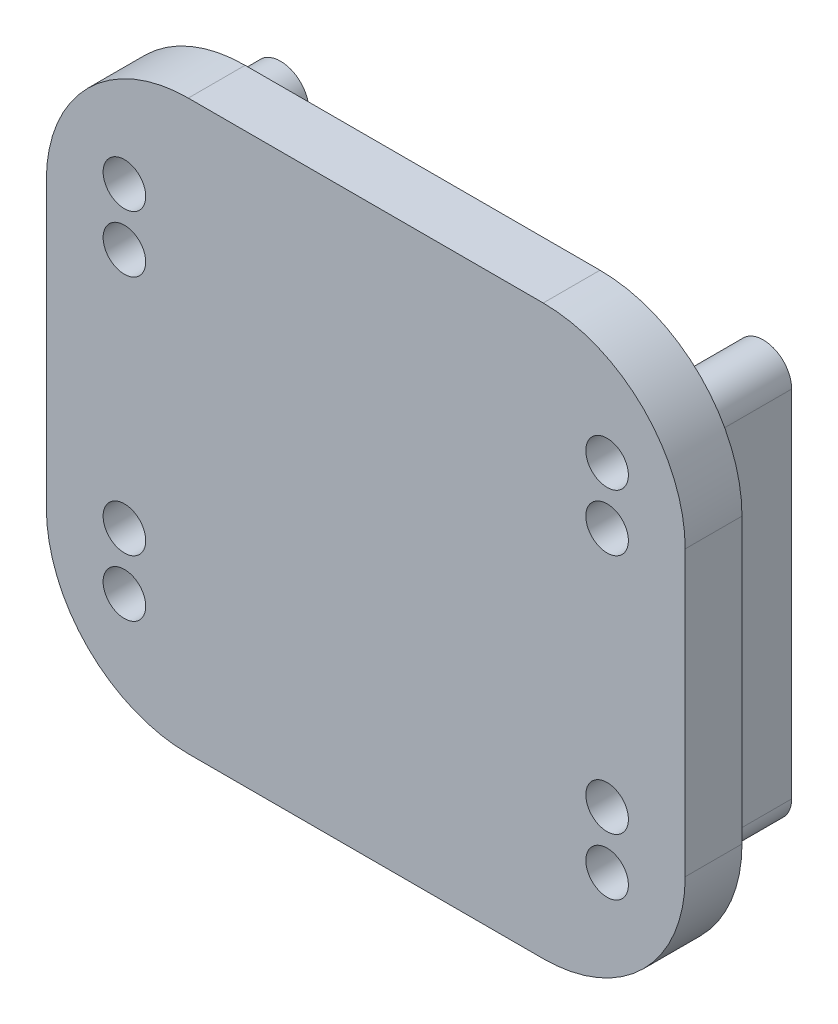
SolidWorks part; units mm, degrees
ref_plane "Front Plane" through (0, 0, 0) normal (0, 0, 1) x (1, 0, 0)
ref_plane "Top Plane" through (0, 0, 0) normal (0, 1, 0) x (1, 0, 0)
ref_plane "Right Plane" through (0, 0, 0) normal (1, 0, 0) x (0, 0, -1)
sketch "Sketch1" plane through (0, 0, 0) normal (0, 0, 1) x (1, 0, 0)
  line L0 (0, 0) -> (0, 25)
  line L1 (30, 0) -> (30, 25)
  line L2 (-4, 25) -> (-4, 0)
  line L3 (34, 25) -> (34, 0)
  arc A0 (-4, 25) -> (0, 25) centre (-2, 25) cw
  arc A1 (-4, 0) -> (0, 0) centre (-2, 0) ccw
  arc A2 (34, 25) -> (30, 25) centre (32, 25) ccw
  arc A3 (34, 0) -> (30, 0) centre (32, 0) cw
  dimension "D1" = 25
  dimension "D2" = 30
  dimension "D3" = 4
  dimension "D4" = 4
extrude "Boss-Extrude1" add sketch "Sketch1" along normal blind 7
sketch "Sketch2" plane through (0, 0, 7) normal (0, 0, 1) x (1, 0, 0)
  line L0 (-4, 12.5) -> (34, 12.5) construction
  line L5 (-4, 25) -> (-4, 0) construction
  line L6 (34, 0) -> (34, 25) construction
  line L8 (-7.5, -7.5) -> (37.5, -7.5)
  line L9 (-7.5, -7.5) -> (-7.5, 32.5)
  line L10 (-7.5, 32.5) -> (37.5, 32.5)
  line L11 (37.5, -7.5) -> (37.5, 32.5)
  line L12 (-7.5, -7.5) -> (37.5, 32.5) construction
  line L13 (-7.5, 32.5) -> (37.5, -7.5) construction
  point P0 (15, 12.5)
  point P10 (15, 12.5)
  dimension "D1" = 45
  dimension "D2" = 40
extrude "Boss-Extrude2" add sketch "Sketch2" along normal blind 4
fillet "Fillet1" radius 10 4 edges at (-7.5, 32.5, 9) (37.5, 32.5, 9) (-7.5, -7.5, 9) (37.5, -7.5, 9)
sketch "Sketch3" plane through (0, 0, 0) normal (0, 0, -1) x (-1, 0, 0)
  line L0 (0, 12.5) -> (-30, 12.5) construction
  line L1 (0, 0) -> (0, 25) construction
  line L2 (-30, 25) -> (-30, 0) construction
  circle A0 centre (-32, 0) radius 1.5
  arc A1 (-34, 0) -> (-30, 0) centre (-32, 0) ccw construction
  circle A4 centre (-32, 4) radius 1.5
  circle A5 centre (2, 0) radius 1.5
  arc A6 (0, 0) -> (4, 0) centre (2, 0) ccw construction
  circle A7 centre (2, 4) radius 1.5
  circle A8 centre (-32, 25) radius 1.5
  circle A9 centre (-32, 21) radius 1.5
  circle A10 centre (2, 25) radius 1.5
  circle A11 centre (2, 21) radius 1.5
  dimension "D1" = 3
  dimension "D2" = 3
  dimension "D4" = 3
  dimension "D5" = 3
  dimension "D3" = 4
extrude "Cut-Extrude1" cut sketch "Sketch3" against normal blind 16
